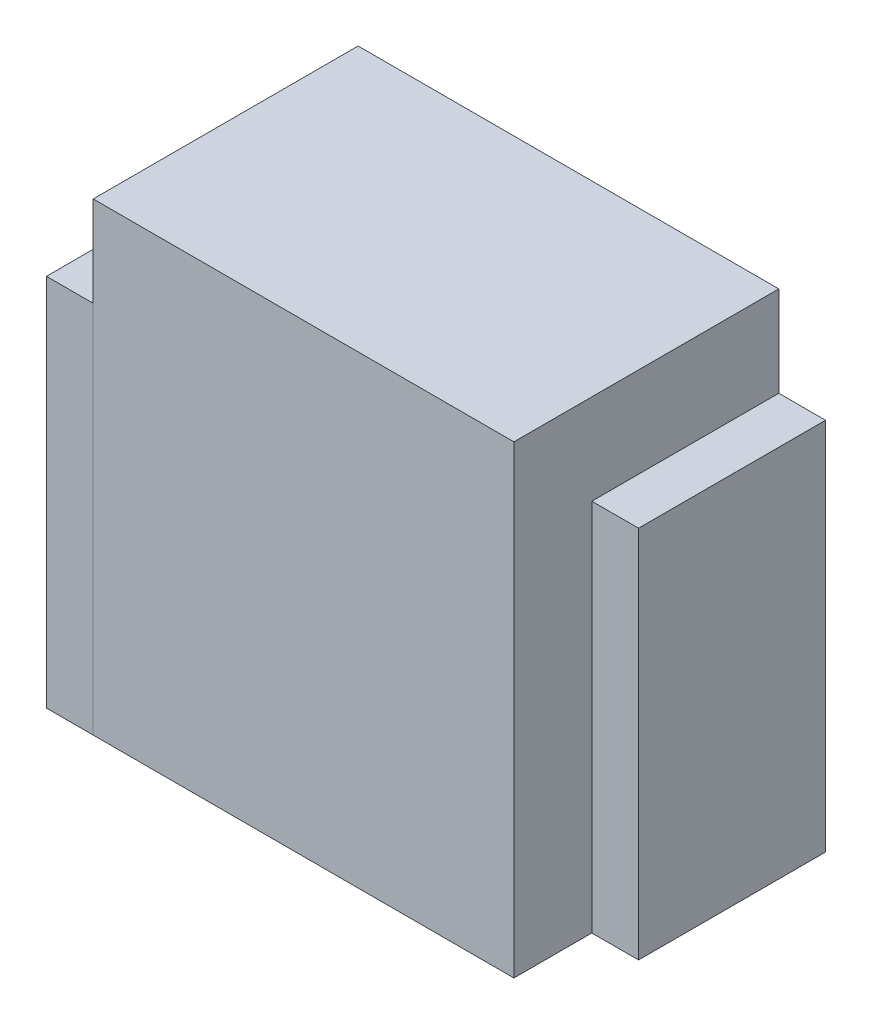
SolidWorks part; units mm, degrees
ref_plane "Front Plane" through (0, 0, 0) normal (0, 0, 1) x (1, 0, 0)
ref_plane "Top Plane" through (0, 0, 0) normal (0, 1, 0) x (1, 0, 0)
ref_plane "Right Plane" through (0, 0, 0) normal (1, 0, 0) x (0, 0, -1)
sketch "Sketch1" plane through (0, 0, 0) normal (0, 1, 0) x (1, 0, 0)
  line L1 (0, 0) -> (270, 0)
  line L2 (0, 0) -> (0, 170)
  line L3 (0, 170) -> (270, 170)
  line L4 (270, 0) -> (270, 170)
  point P4 (0, 0)
extrude "Boss-Extrude1" add sketch "Sketch1" along normal blind 298
sketch "Sketch2" plane through (0, 0, 0) normal (-1, 0, 0) x (0, 0, 1)
  line L1 (-170, 0) -> (-50, 0)
  line L2 (-170, 0) -> (-170, 240)
  line L3 (-170, 240) -> (-50, 240)
  line L4 (-50, 0) -> (-50, 240)
  line L5 (-45, 240) -> (0, 240)
  line L6 (-45, 240) -> (-45, 0)
  line L7 (-45, 0) -> (0, 0)
  line L8 (0, 240) -> (0, 0)
extrude "Boss-Extrude2" add sketch "Sketch2" along normal blind 30 separate body
sketch "Sketch3" plane through (270, 0, 0) normal (1, 0, 0) x (0, 0, -1)
  line L1 (170, 0) -> (50, 0)
  line L2 (170, 0) -> (170, 240)
  line L3 (170, 240) -> (50, 240)
  line L4 (50, 0) -> (50, 240)
extrude "Boss-Extrude3" add sketch "Sketch3" along normal blind 30 separate body
